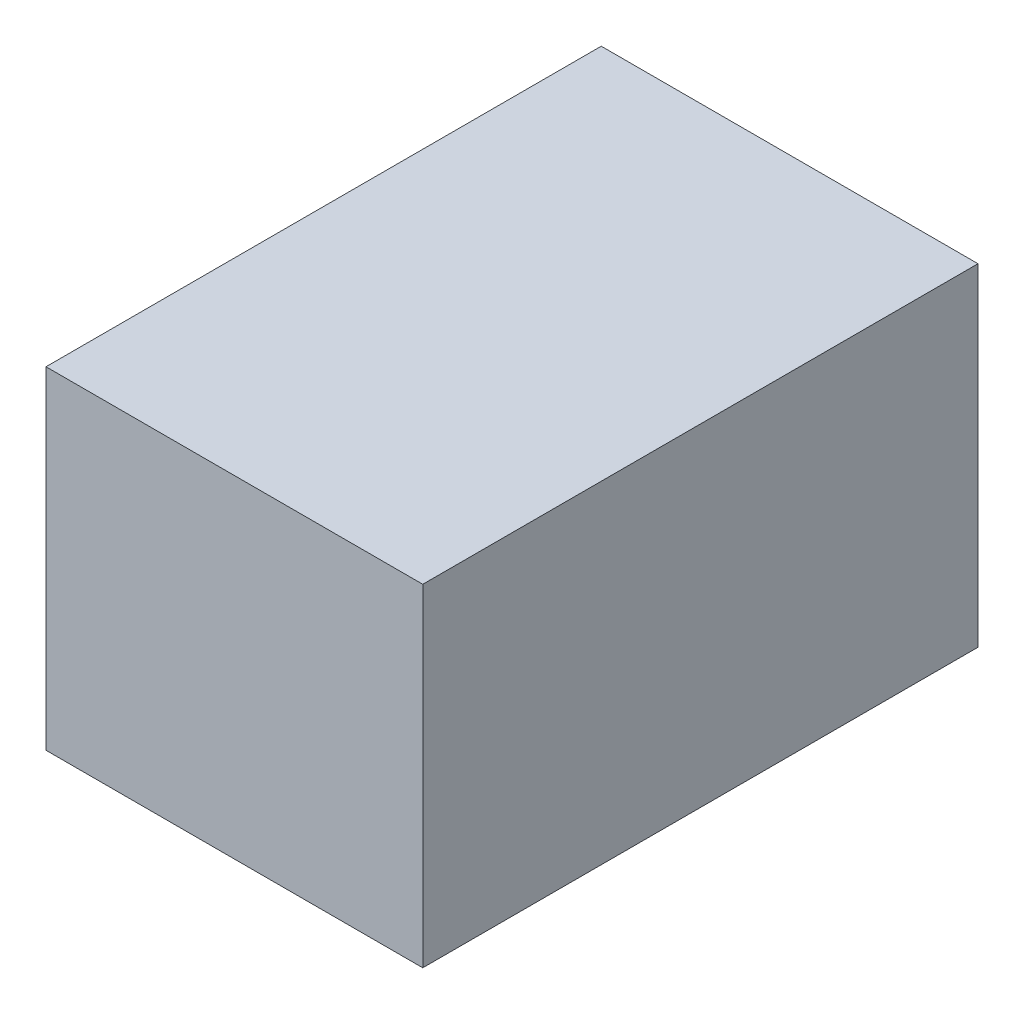
SolidWorks part; units mm, degrees
material "ABS"
ref_plane "Front Plane" through (0, 0, 0) normal (0, 0, 1) x (1, 0, 0)
ref_plane "Top Plane" through (0, 0, 0) normal (0, 1, 0) x (1, 0, 0)
ref_plane "Right Plane" through (0, 0, 0) normal (1, 0, 0) x (0, 0, -1)
sketch "Sketch1" plane through (0, 0, 0) normal (0, 0, 1) x (1, 0, 0)
  line L1 (-19, -16.75) -> (19, -16.75)
  line L2 (-19, -16.75) -> (-19, 16.75)
  line L3 (-19, 16.75) -> (19, 16.75)
  line L4 (19, -16.75) -> (19, 16.75)
  line L5 (-19, -16.75) -> (19, 16.75) construction
  line L6 (-19, 16.75) -> (19, -16.75) construction
  point P0 (0, 0)
  dimension "D1" = 38
  dimension "D2" = 33.5
extrude "Boss-Extrude1" add sketch "Sketch1" along normal blind 56
